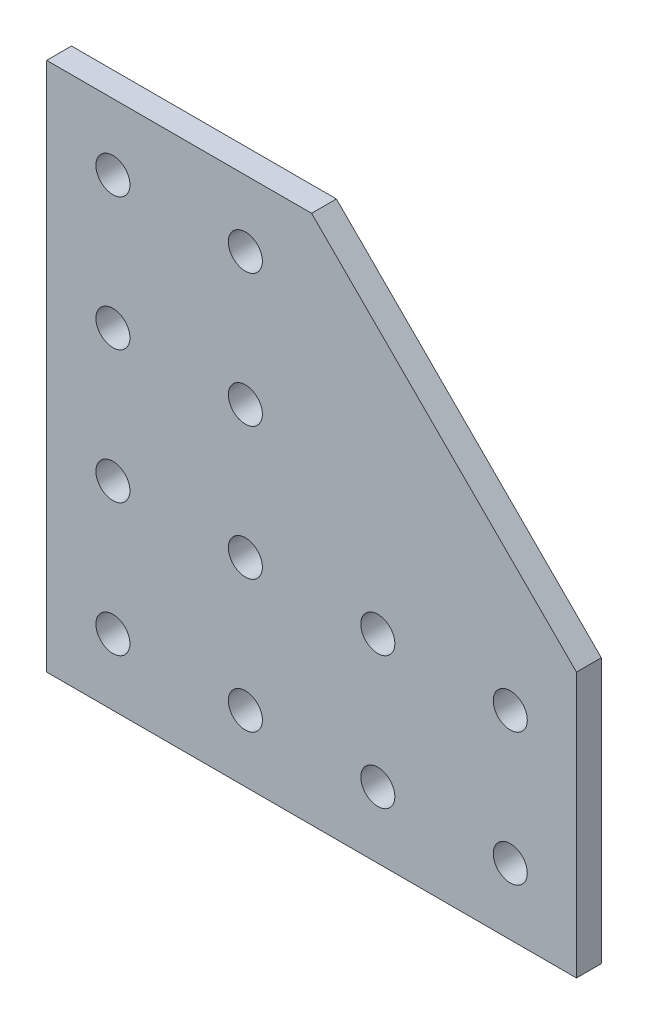
SolidWorks part; units mm, degrees
ref_plane "Front Plane" through (0, 0, 0) normal (0, 0, 1) x (1, 0, 0)
ref_plane "Top Plane" through (0, 0, 0) normal (0, 1, 0) x (1, 0, 0)
ref_plane "Right Plane" through (0, 0, 0) normal (1, 0, 0) x (0, 0, -1)
sketch "Sketch1" plane through (0, 0, 0) normal (0, 0, 1) x (1, 0, 0)
  line L0 (0, 0) -> (0, 101.6)
  line L1 (12.7, 12.7) -> (38.1, 12.7) construction
  line L2 (38.1, 12.7) -> (63.5, 12.7) construction
  line L3 (12.7, 12.7) -> (12.7, 38.1) construction
  line L4 (101.6, 50.8) -> (50.8, 101.6)
  line L5 (101.6, 0) -> (0, 0)
  line L6 (12.7, 38.1) -> (12.7, 63.5) construction
  line L7 (101.6, 50.8) -> (101.6, 0)
  line L8 (0, 101.6) -> (50.8, 101.6)
  line L9 (63.5, 12.7) -> (88.9, 12.7) construction
  line L10 (88.9, 12.7) -> (88.9, 38.1) construction
  line L11 (88.9, 38.1) -> (63.5, 38.1) construction
  line L12 (63.5, 38.1) -> (63.5, 12.7) construction
  line L13 (63.5, 38.1) -> (38.1, 38.1) construction
  line L14 (38.1, 38.1) -> (38.1, 12.7) construction
  line L15 (38.1, 38.1) -> (12.7, 38.1) construction
  line L16 (12.7, 63.5) -> (12.7, 88.9) construction
  line L17 (12.7, 88.9) -> (38.1, 88.9) construction
  line L18 (38.1, 88.9) -> (38.1, 63.5) construction
  line L19 (38.1, 63.5) -> (38.1, 38.1) construction
  line L20 (38.1, 63.5) -> (12.7, 63.5) construction
  circle A0 centre (12.7, 12.7) radius 3.2639
  circle A1 centre (38.1, 12.7) radius 3.2639
  circle A2 centre (63.5, 12.7) radius 3.2639
  circle A3 centre (12.7, 38.1) radius 3.2639
  circle A4 centre (12.7, 63.5) radius 3.2639
  circle A5 centre (88.9, 12.7) radius 3.2639
  circle A6 centre (88.9, 38.1) radius 3.2639
  circle A7 centre (63.5, 38.1) radius 3.2639
  circle A8 centre (38.1, 38.1) radius 3.2639
  circle A9 centre (12.7, 88.9) radius 3.2639
  circle A10 centre (38.1, 88.9) radius 3.2639
  circle A11 centre (38.1, 63.5) radius 3.2639
  dimension "D1" = 25.4
  dimension "E" = 6.5278
  dimension "D2" = 12.7
  dimension "C" = 50.8
  dimension "D3" = 12.7
  dimension "B" = 101.6
extrude "Boss-Extrude1" add sketch "Sketch1" along normal mid plane 4.7625
